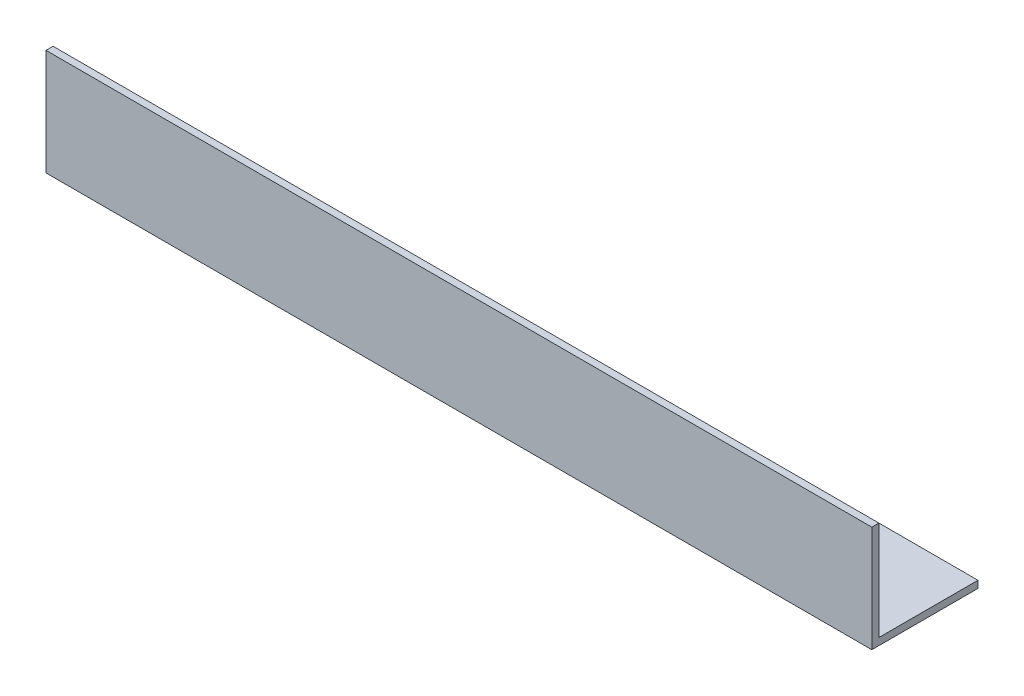
SolidWorks part; units mm, degrees
ref_plane "Спереди" through (0, 0, 0) normal (0, 0, 1) x (1, 0, 0)
ref_plane "Сверху" through (0, 0, 0) normal (0, 1, 0) x (1, 0, 0)
ref_plane "Справа" through (0, 0, 0) normal (1, 0, 0) x (0, 0, -1)
sketch "Эскиз1" plane through (0, 0, 0) normal (1, 0, 0) x (0, 0, -1)
  line L0 (0, 0) -> (0, 45)
  line L1 (0, 0) -> (45, 0)
  dimension "D1" = 45
extrude "Вытянуть-Тонкостенный1" add sketch "Эскиз1" along normal blind 350 thin
